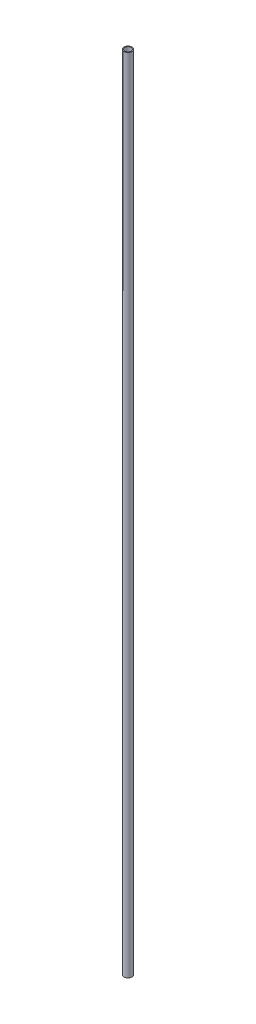
SolidWorks part; units mm, degrees
ref_plane "Front Plane" through (0, 0, 0) normal (0, 0, 1) x (1, 0, 0)
ref_plane "Top Plane" through (0, 0, 0) normal (0, 1, 0) x (1, 0, 0)
ref_plane "Right Plane" through (0, 0, 0) normal (1, 0, 0) x (0, 0, -1)
sketch "Sketch1" plane through (0, 0, 0) normal (0, 1, 0) x (1, 0, 0)
  circle A0 centre (0, 0) radius 5
  circle A1 centre (0, 0) radius 4
  dimension "D1" = 8
  dimension "D2" = 10
extrude "Boss-Extrude1" add sketch "Sketch1" along normal blind 1000
